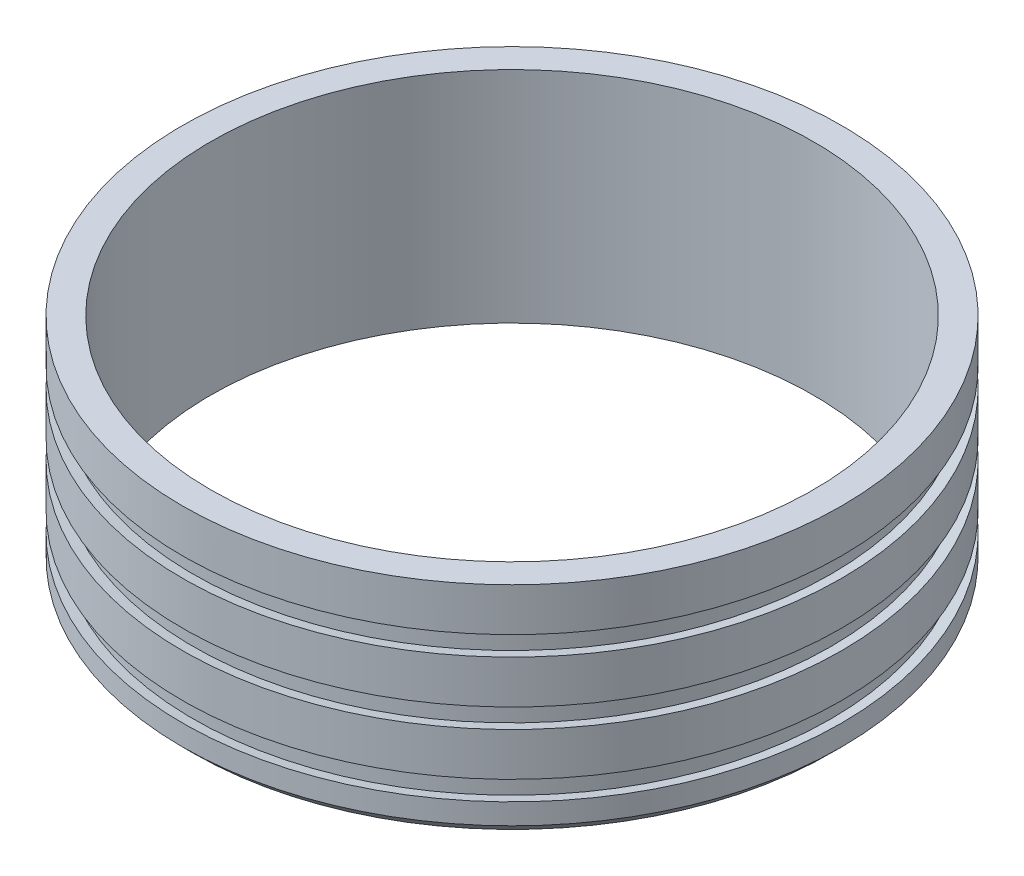
SolidWorks part; units mm, degrees
material "ABS"
ref_plane "Front Plane" through (0, 0, 0) normal (0, 0, 1) x (1, 0, 0)
ref_plane "Top Plane" through (0, 0, 0) normal (0, 1, 0) x (1, 0, 0)
ref_plane "Right Plane" through (0, 0, 0) normal (1, 0, 0) x (0, 0, -1)
sketch "Sketch1" plane through (0, 0, 0) normal (0, 1, 0) x (1, 0, 0)
  circle A0 centre (0, 0) radius 76.25
  circle A1 centre (0, 0) radius 69.75
  dimension "D2" = 152.5
  dimension "D1" = 6.5
extrude "Boss-Extrude1" add sketch "Sketch1" along normal blind 50.8
sketch "Sketch2" plane through (0, 0, 0) normal (0, 0, 1) x (1, 0, 0)
  line L0 (-76.25, 40.8) -> (-76.25, 36.3) construction
  line L1 (-76.25, 40.8) -> (-76.25, 36.3)
  line L2 (-76.25, 50.8) -> (-76.25, 0) construction
  line L19 (0, 0) -> (0, 50.8) construction
  line L20 (-76.25, 0) -> (76.25, 0) construction
  line L21 (69.75, 50.8) -> (-69.75, 50.8) construction
  line L22 (-76.25, 40.8) -> (-73.75, 41.2408)
  line L23 (-73.75, 41.2408) -> (-73.75, 35.8592)
  line L24 (-73.75, 38.55) -> (-76.25, 38.55) construction
  line L25 (-76.25, 36.3) -> (-73.75, 35.8592)
  line L26 (-73.75, 26.7408) -> (-73.75, 21.3592)
  line L27 (-76.25, 21.8) -> (-73.75, 21.3592)
  line L28 (-76.25, 26.3) -> (-76.25, 21.8)
  line L29 (-76.25, 26.3) -> (-73.75, 26.7408)
  line L30 (-73.75, 12.2408) -> (-73.75, 6.8592)
  line L31 (-76.25, 7.3) -> (-73.75, 6.8592)
  line L32 (-76.25, 11.8) -> (-76.25, 7.3)
  line L33 (-76.25, 11.8) -> (-73.75, 12.2408)
  dimension "D2" = 2.5
  dimension "D3" = 100
  dimension "D1" = 4.5
  dimension "D5" = 10
  dimension "D6" = 10
  dimension "D4" = 3
revolve "Cut-Revolve1" cut sketch "Sketch2" angle 360 about L19
chamfer "Chamfer1" distance 2.5 angle 45 1 edges at (0, 0, 76.25)
